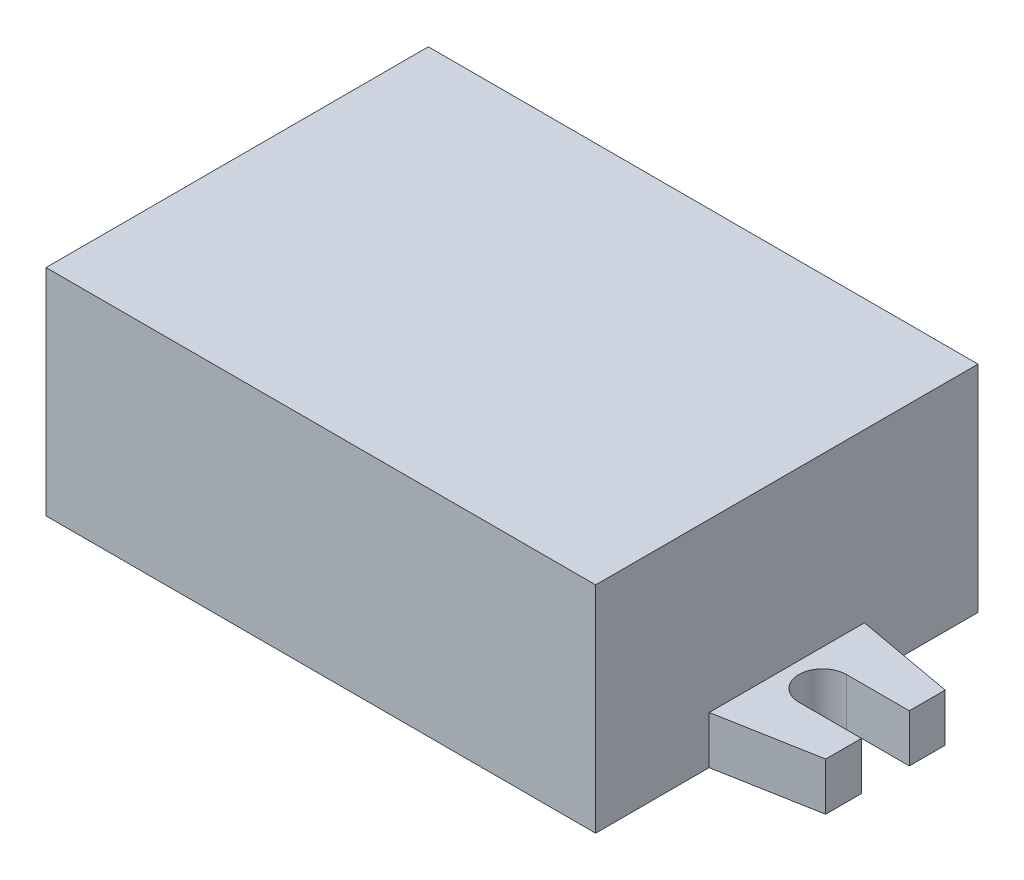
SolidWorks part; units mm, degrees
ref_plane "Front Plane" through (0, 0, 0) normal (0, 0, 1) x (1, 0, 0)
ref_plane "Top Plane" through (0, 0, 0) normal (0, 1, 0) x (1, 0, 0)
ref_plane "Right Plane" through (0, 0, 0) normal (1, 0, 0) x (0, 0, -1)
sketch "Sketch1" plane through (0, 0, 0) normal (0, 1, 0) x (1, 0, 0)
  line L0 (0, -16) -> (0, 16)
  line L1 (0, 16) -> (-23, 16)
  line L2 (-23, 16) -> (-23, -16)
  line L3 (-23, -16) -> (0, -16)
  point P4 (0, 0)
  dimension "D1" = 23
  dimension "D2" = 32
extrude "Boss-Extrude1" add sketch "Sketch1" along normal blind 18
sketch "Sketch2" plane through (0, 0, 0) normal (0, -1, 0) x (1, 0, 0)
  line L0 (0, 0) -> (-37.8119, 0) construction
  line L11 (-31.25, 2) -> (-31.25, -2) construction
  line L12 (-31.25, -5) -> (-31.25, -2)
  line L13 (-31.25, 5) -> (-23, 6.5)
  line L14 (-23, -16) -> (-23, 16) construction
  line L15 (-31.25, -5) -> (-23, -6.5)
  line L16 (-23, 6.5) -> (-23, -6.5)
  line L17 (-31.25, 2) -> (-26, 2)
  line L18 (-31.25, -2) -> (-26, -2)
  line L19 (-31.25, 2) -> (-31.25, 5)
  arc A1 (-26, 2) -> (-26, -2) centre (-26, 0) cw
  point P6 (-37.8119, 0)
  point P7 (-31.25, 0)
  point P15 (-31.25, 0)
  dimension "D6" = 3
  dimension "D1" = 13
  dimension "D2" = 10
  dimension "D3" = 8.25
  dimension "D4" = 4
  dimension "D5" = 3
extrude "Boss-Extrude2" add sketch "Sketch2" against normal blind 4
mirror "Mirror1" about plane through (0, 18, 16) normal (-1, 0, 0) of "Boss-Extrude1", "Boss-Extrude2"
